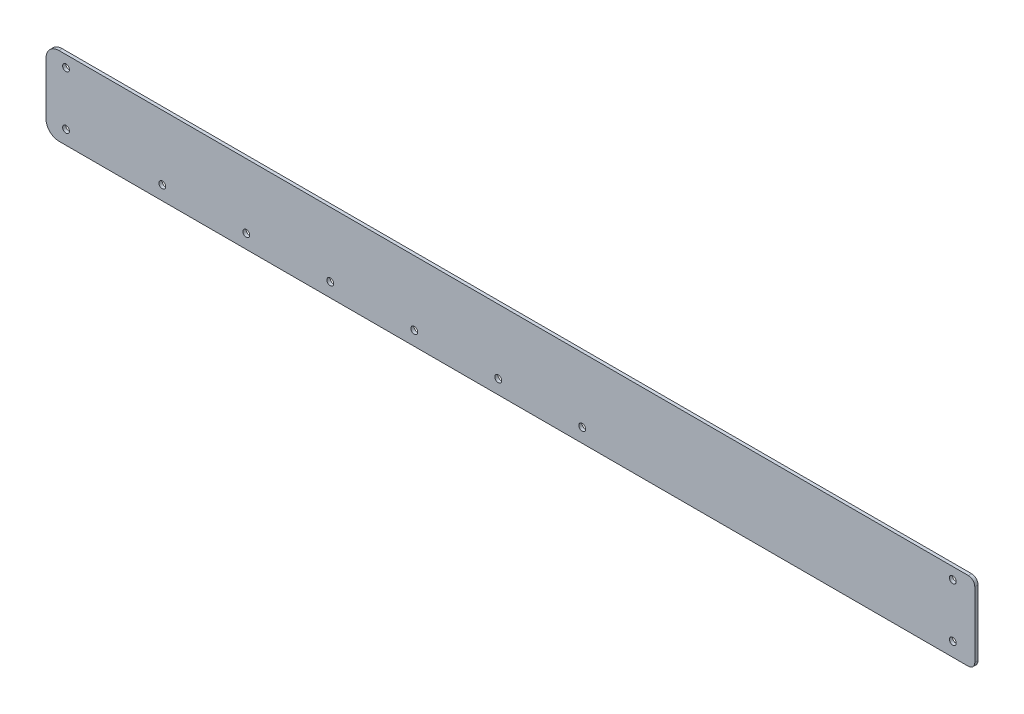
SolidWorks part; units mm, degrees
ref_plane "Plan de face" through (0, 0, 0) normal (0, 0, 1) x (1, 0, 0)
ref_plane "Plan de dessus" through (0, 0, 0) normal (0, 1, 0) x (1, 0, 0)
ref_plane "Plan de droite" through (0, 0, 0) normal (1, 0, 0) x (0, 0, -1)
sketch "Model" plane through (0, 0, 0) normal (0, 0, 1) x (1, 0, 0)
  line L0 (370.8894, 211.9685) -> (-192.1275, 211.9685)
  line L1 (374.8894, 207.9685) -> (374.8894, 167.3055)
  line L2 (-192.1275, 163.3055) -> (370.8894, 163.3055)
  line L3 (-200.1275, 171.3055) -> (-200.1275, 203.9685)
  circle A0 centre (361.2894, 204.9227) radius 2.1
  circle A1 centre (-187.7242, 204.9227) radius 2.1
  circle A2 centre (-76.1369, 171.9227) radius 2.1
  circle A3 centre (-24.1369, 171.9227) radius 2.1
  circle A4 centre (-128.1369, 171.9227) radius 2.1
  circle A5 centre (131.8631, 171.9227) radius 2.1
  circle A6 centre (79.8631, 171.9227) radius 2.1
  circle A7 centre (27.8631, 171.9227) radius 2.1
  circle A8 centre (361.2894, 171.9227) radius 2.1
  circle A9 centre (-187.7242, 171.9227) radius 2.1
  arc A10 (374.8894, 207.9685) -> (370.8894, 211.9685) centre (370.8894, 207.9685) ccw
  arc A11 (370.8894, 163.3055) -> (374.8894, 167.3055) centre (370.8894, 167.3055) ccw
  arc A12 (-192.1275, 211.9685) -> (-200.1275, 203.9685) centre (-192.1275, 203.9685) ccw
  arc A13 (-200.1275, 171.3055) -> (-192.1275, 163.3055) centre (-192.1275, 171.3055) ccw
extrude "Boss.-Extru.1" add sketch "Model" along normal blind 2
